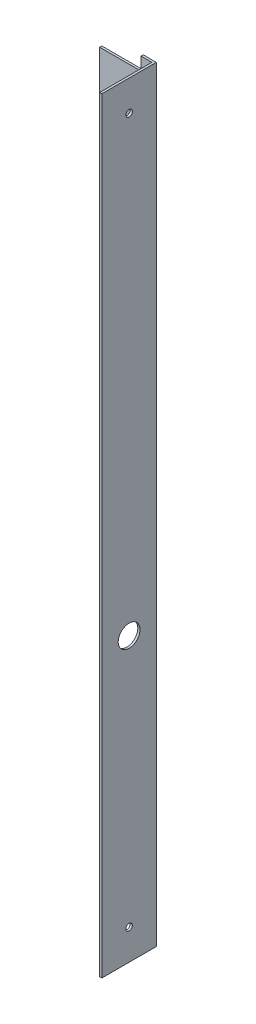
SolidWorks part; units mm, degrees
material "Aleación 1060"
ref_plane "Alzado" through (0, 0, 0) normal (0, 0, 1) x (1, 0, 0)
ref_plane "Planta" through (0, 0, 0) normal (0, 1, 0) x (1, 0, 0)
ref_plane "Vista lateral" through (0, 0, 0) normal (1, 0, 0) x (0, 0, -1)
sketch "Croquis1" plane through (0, 0, 0) normal (0, 0, 1) x (1, 0, 0)
  line L1 (-56.34, 62.1804) -> (-61.34, 62.1804)
  line L2 (-56.34, -289.8196) -> (-56.34, 62.1804)
  line L5 (-61.34, 62.1804) -> (-61.34, 56.1804)
  line L9 (-61.34, 56.1804) -> (-80.34, 56.1804)
  line L10 (-80.34, 56.1804) -> (-80.34, -13.8196)
  line L11 (-80.34, -13.8196) -> (-61.34, -13.8196)
  line L12 (-61.34, -13.8196) -> (-61.34, -213.8196)
  line L13 (-61.34, -213.8196) -> (-80.34, -213.8196)
  line L14 (-80.34, -213.8196) -> (-80.34, -283.8196)
  line L15 (-80.34, -283.8196) -> (-61.34, -283.8196)
  line L16 (-61.34, -283.8196) -> (-61.34, -289.8196)
  line L17 (-61.34, -289.8196) -> (-56.34, -289.8196)
  dimension "D1" = 352
  dimension "D4" = 200
  dimension "D2" = 6
  dimension "D3" = 6
sketch "Croquis2" plane through (0, 0, 0) normal (0, 0, 1) x (1, 0, 0)
  line L1 (-56.34, 62.1804) -> (-55.34, 62.1804)
  line L2 (-56.34, 62.1804) -> (-56.34, -289.8196)
  line L3 (-56.34, -289.8196) -> (-55.34, -289.8196)
  line L4 (-55.34, 62.1804) -> (-55.34, -289.8196)
  dimension "D1" = 1
  dimension "D2" = 352
extrude "Saliente-Extruir2" add sketch "Croquis2" along normal blind 25
sketch "Croquis5" plane through (-55.34, 0, 0) normal (1, 0, 0) x (0, 0, -1)
  line L0 (-25, 62.1804) -> (0, 62.1804) construction
  line L1 (-25, -289.8196) -> (0, -289.8196) construction
  line L2 (-25, -289.8196) -> (-25, 62.1804) construction
  circle A0 centre (-12.5, 48.1804) radius 1.5
  circle A1 centre (-12.5, -275.8196) radius 1.5
  circle A2 centre (-12.5, -159.8196) radius 5
  dimension "D1" = 14
  dimension "D4" = 12.5
  dimension "D5" = 12.5
  dimension "D2" = 14
  dimension "D3" = 12.5
  dimension "D6" = 130
extrude "Cortar-Extruir2" cut sketch "Croquis5" against normal blind 1
extrude "Saliente-Extruir3" add sketch "Croquis1" along normal blind 1
